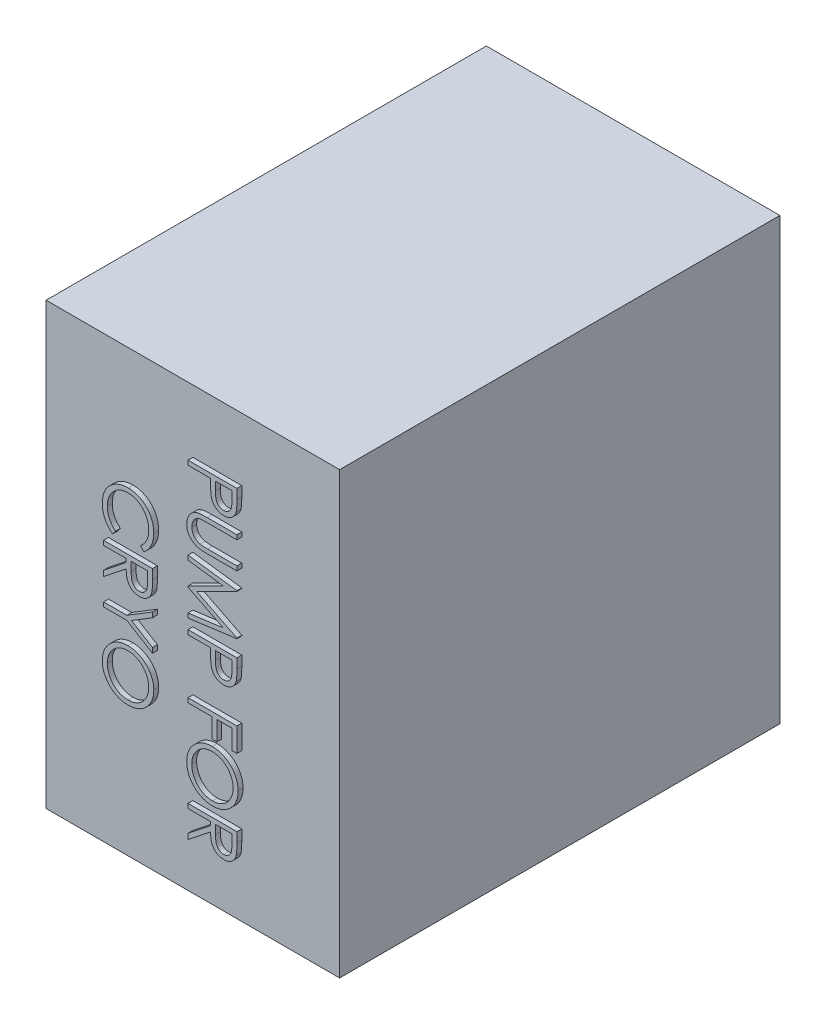
SolidWorks part; units mm, degrees
ref_plane "Front Plane" through (0, 0, 0) normal (0, 0, 1) x (1, 0, 0)
ref_plane "Top Plane" through (0, 0, 0) normal (0, 1, 0) x (1, 0, 0)
ref_plane "Right Plane" through (0, 0, 0) normal (1, 0, 0) x (0, 0, -1)
sketch "Sketch1" plane through (0, 0, 0) normal (0, 0, 1) x (1, 0, 0)
  line L1 (0, 0) -> (-300, 0)
  line L2 (0, 0) -> (0, -450)
  line L3 (0, -450) -> (-300, -450)
  line L4 (-300, 0) -> (-300, -450)
  dimension "D1" = 300
  dimension "D2" = 450
extrude "Boss-Extrude1" add sketch "Sketch1" along normal blind 450
sketch "Sketch2" plane through (0, 0, 450) normal (0, 0, 1) x (1, 0, 0)
  line L0 (-150, 0) -> (-150, -456.9404) construction
  line L1 (0, 0) -> (-300, 0) construction
  text T0 "   PUMP FOR\r\n      CRYO" font "Century Gothic" height 50
extrude "Boss-Extrude2" add sketch "Sketch2" along normal blind 5
